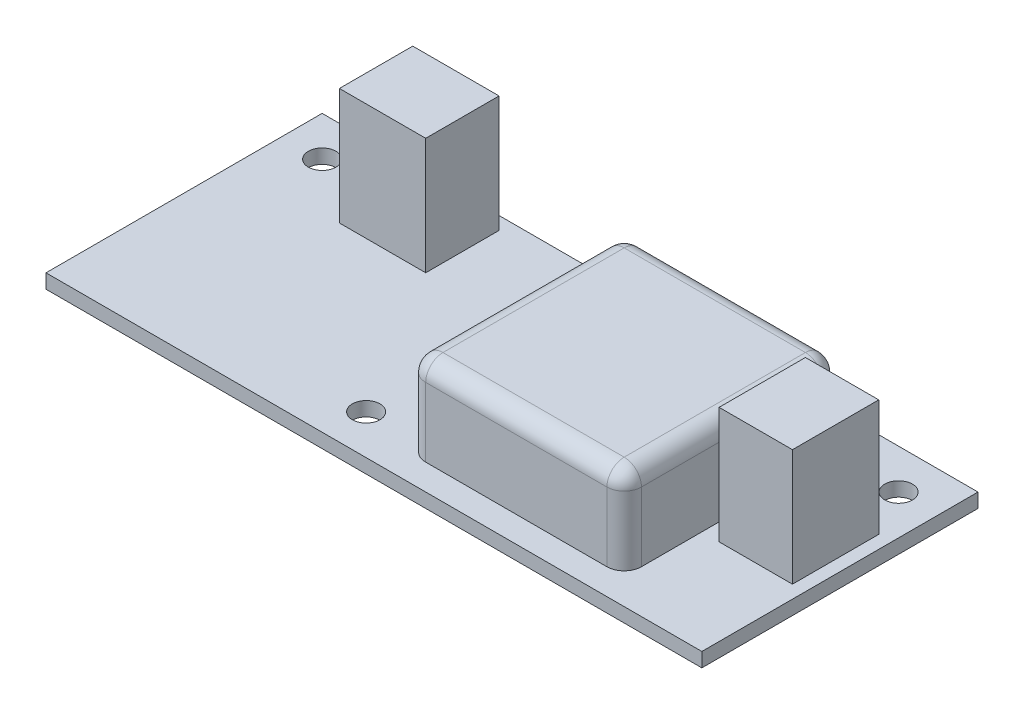
SolidWorks part; units mm, degrees
ref_plane "Front Plane" through (0, 0, 0) normal (0, 0, 1) x (1, 0, 0)
ref_plane "Top Plane" through (0, 0, 0) normal (0, 1, 0) x (1, 0, 0)
ref_plane "Right Plane" through (0, 0, 0) normal (1, 0, 0) x (0, 0, -1)
sketch "Sketch1" plane through (0, 0, 0) normal (0, 1, 0) x (1, 0, 0)
  line L1 (0, 0) -> (76, 0)
  line L2 (0, 0) -> (0, 32)
  line L3 (0, 32) -> (76, 32)
  line L4 (76, 0) -> (76, 32)
  dimension "D1" = 76
  dimension "D2" = 32
extrude "Boss-Extrude1" add sketch "Sketch1" along normal blind 1.65 contours L3 L4 L1 L2
hole_wizard "M3 Clearance Hole1" positions "Sketch2" profile "Sketch3" hole size "M3" standard "ISO"
sketch "Sketch2" plane through (0, 1.65, 0) normal (0, 1, 0) x (1, 0, 0)
  line L0 (0, 0) -> (0, 32) construction
  line L1 (76, 0) -> (76, 32) construction
  line L2 (0, 0) -> (76, 0) construction
  line L3 (0, 32) -> (76, 32) construction
  point P0 (71.4, 27.4)
  point P2 (32.5, 4.6)
  point P4 (4.6, 27.4)
  dimension "D1" = 4.6
  dimension "D2" = 4.6
  dimension "D3" = 4.6
  dimension "D4" = 32.5
  dimension "D5" = 4.6
sketch "Sketch3" plane through (71.4, 1.65, -27.4) normal (1, 0, 0) x (0, 0, 1)
  line L0 (0, 0) -> (0, 20.9614)
  line L1 (0, 20.9614) -> (1.6, 20)
  line L2 (1.6, 20) -> (1.6, 0)
  line L5 (1.6, 0) -> (0, 0)
  line L10 (0, 20.9614) -> (-1.6, 20) construction
  line L11 (0, -6.35) -> (0, 107.95) construction
  dimension "Hole Dia." = 3.2
  dimension "Hole Depth" = 20
  dimension "Drill Angle" = 118
sketch "Sketch4" plane through (0, 1.65, 0) normal (0, 1, 0) x (1, 0, 0)
  line L0 (0, 32) -> (76, 32) construction
  line L1 (12, 30.5) -> (22, 30.5)
  line L2 (12, 30.5) -> (12, 22)
  line L3 (12, 22) -> (22, 22)
  line L4 (22, 30.5) -> (22, 22)
  line L5 (66, 22) -> (74.5, 22)
  line L6 (66, 22) -> (66, 12)
  line L7 (66, 12) -> (74.5, 12)
  line L8 (74.5, 22) -> (74.5, 12)
  line L9 (0, 0) -> (0, 32) construction
  line L10 (76, 0) -> (76, 32) construction
  dimension "D1" = 10
  dimension "D2" = 8.5
  dimension "D3" = 1.5
  dimension "D4" = 12
  dimension "D5" = 10
  dimension "D6" = 1.5
extrude "Boss-Extrude2" add sketch "Sketch4" along normal blind 13.5
sketch "Sketch5" plane through (0, 1.65, 0) normal (0, 1, 0) x (1, 0, 0)
  line L0 (76, 0) -> (76, 32) construction
  line L1 (39, 3) -> (64, 3)
  line L2 (39, 3) -> (39, 28)
  line L3 (39, 28) -> (64, 28)
  line L4 (64, 3) -> (64, 28)
  line L5 (39, 3) -> (64, 28) construction
  line L6 (39, 28) -> (64, 3) construction
  line L7 (0, 32) -> (76, 32) construction
  point P0 (51.5, 15.5)
  dimension "D1" = 25
  dimension "D2" = 12
  dimension "D3" = 4
extrude "Boss-Extrude3" add sketch "Sketch5" along normal blind 10
fillet "Fillet1" radius 2 8 edges at (39, 11.65, -15.5) (51.5, 11.65, -28) (64, 11.65, -15.5) (51.5, 11.65, -3) (64, 6.65, -3) (39, 6.65, -3) (39, 6.65, -28) (64, 6.65, -28)
